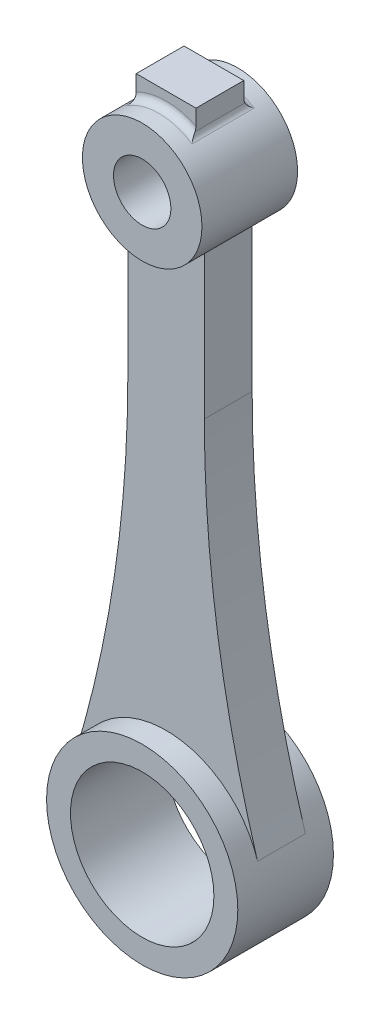
SolidWorks part; units mm, degrees
material "Plain Carbon Steel"
ref_plane "Front Plane" through (0, 0, 0) normal (0, 0, 1) x (1, 0, 0)
ref_plane "Top Plane" through (0, 0, 0) normal (0, 1, 0) x (1, 0, 0)
ref_plane "Right Plane" through (0, 0, 0) normal (1, 0, 0) x (0, 0, -1)
sketch "Sketch3" plane through (0, 0, 0) normal (0, 0, 1) x (1, 0, 0)
  circle A0 centre (0, 0) radius 20
  circle A1 centre (0, 0) radius 15
  circle A2 centre (0, 120) radius 12.5
  circle A3 centre (0, 120) radius 6
  dimension "D1" = 40
  dimension "D2" = 30
  dimension "D3" = 25
  dimension "D4" = 12
  dimension "D5" = 120
extrude "Boss-Extrude3" add sketch "Sketch3" along normal mid plane 20
sketch "Sketch4" plane through (0, 0, 0) normal (0, 0, 1) x (1, 0, 0)
  line L0 (0, 120) -> (0, 79.9136) construction
  line L1 (8, 110.3953) -> (8, 80.3953)
  line L2 (-8, 110.3953) -> (-8, 80.3953)
  circle A0 centre (0, 0) radius 20 construction
  circle A1 centre (0, 120) radius 12.5 construction
  arc A2 (19.1283, 5.8404) -> (-19.1283, 5.8404) centre (0, 0) ccw
  arc A3 (-8, 110.3953) -> (8, 110.3953) centre (0, 120) ccw
  arc A4 (8, 80.3953) -> (19.1283, 5.8404) centre (263.3086, 80.3953) ccw
  arc A5 (-8, 80.3953) -> (-19.1283, 5.8404) centre (-263.3086, 80.3953) cw
  dimension "D1" = 30
  dimension "D2" = 8
extrude "Boss-Extrude4" add sketch "Sketch4" along normal mid plane 10
sketch "Sketch5" plane through (0, 0, 0) normal (0, 0, 1) x (1, 0, 0)
  line L0 (0, 146.7255) -> (0, -34.2436) construction
  line L1 (-6.25, 135.8253) -> (-6.25, 130.8253)
  line L2 (6.25, 135.8253) -> (6.25, 130.8253)
  line L3 (-6.25, 135.8253) -> (6.25, 135.8253)
  circle A0 centre (0, 120) radius 12.5 construction
  arc A1 (6.25, 130.8253) -> (-6.25, 130.8253) centre (0, 120) ccw
  point P10 (-6.25, 133.3253)
  point P11 (6.25, 133.3253)
  dimension "D1" = 5
  dimension "D2" = 12.5
extrude "Boss-Extrude5" add sketch "Sketch5" along normal mid plane 10
fillet "Fillet1" radius 1.5 4 edges at (-6.25, 130.8253, 0) (0, 132.5, -5) (0, 132.5, 5) (6.25, 130.8253, 0)
